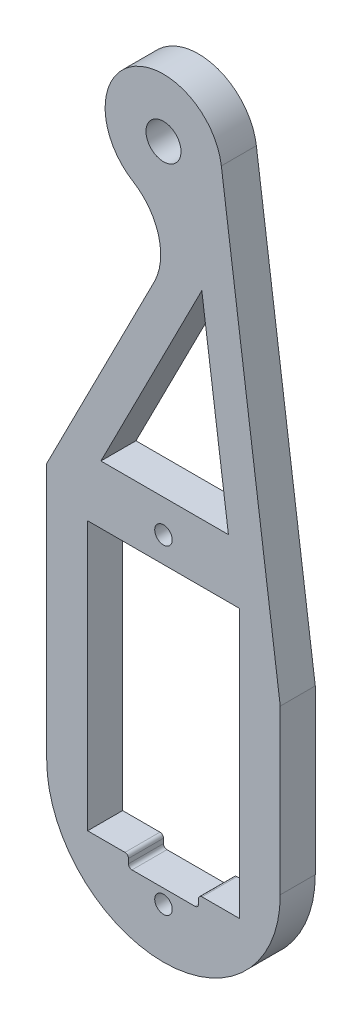
SolidWorks part; units mm, degrees
ref_plane "前视基准面" through (0, 0, 0) normal (0, 0, 1) x (1, 0, 0)
ref_plane "上视基准面" through (0, 0, 0) normal (0, 1, 0) x (1, 0, 0)
ref_plane "右视基准面" through (0, 0, 0) normal (1, 0, 0) x (0, 0, -1)
sketch "草图1" plane through (0, 0, 0) normal (0, 0, 1) x (1, 0, 0)
  line L0 (0, 0) -> (18.9934, 0) construction
  line L1 (-6.5, 11.5) -> (6.5, 11.5)
  line L2 (-6.5, 11.5) -> (-6.5, -11.5)
  line L3 (-6.5, -11.5) -> (6.5, -11.5)
  line L4 (6.5, 11.5) -> (6.5, -11.5)
  line L5 (-6.5, 11.5) -> (6.5, -11.5) construction
  line L6 (-6.5, -11.5) -> (6.5, 11.5) construction
  line L7 (0, 0) -> (0, 13.7) construction
  line L8 (0, -8) -> (0, 0) construction
  line L9 (0, 42.88) -> (0, 0) construction
  line L10 (10, -8) -> (10, 6)
  line L11 (10, 6) -> (4.9555, 43.5458)
  line L12 (-10, -8) -> (-10, 14)
  line L13 (-10, 14) -> (-0.7821, 32.0911)
  line L14 (-5.3592, 16.5) -> (3.2833, 33.462)
  line L15 (5.5623, 16.5) -> (3.2833, 33.462)
  line L16 (-7.327, 12.638) -> (1.8909, 30.7291) construction
  line L17 (7.0267, 5.6005) -> (1.9822, 43.1463) construction
  line L18 (-5.3592, 16.5) -> (5.5623, 16.5)
  line L19 (-6.5, 16.5) -> (6.5, 16.5) construction
  circle A0 centre (0, 13.7) radius 0.75
  circle A1 centre (0, -13.7) radius 0.75
  arc A2 (-10, -8) -> (10, -8) centre (0, -8) ccw
  arc A3 (4.9555, 43.5458) -> (0, 37.88) centre (0, 42.88) ccw
  circle A4 centre (0, -5.12) radius 4 construction
  arc A5 (-0.7821, 32.0911) -> (-2.6186, 38.6205) centre (-5.2372, 34.3611) ccw
  circle A6 centre (0, 42.88) radius 1.5
  point P0 (0, 0)
  point P13 (0, 0)
  dimension "D3" = 1.5
  dimension "D5" = 10
  dimension "D7" = 10
  dimension "D10" = 8
  dimension "D13" = 10
  dimension "D14" = 63
  dimension "D18" = 3
  dimension "D1" = 23
  dimension "D2" = 13
  dimension "D4" = 27.4
  dimension "D6" = 8
  dimension "D8" = 6.38
  dimension "D9" = 48
  dimension "D11" = 14
  dimension "D12" = 22
  dimension "D15" = 3
  dimension "D16" = 3
  dimension "D17" = 5
extrude "凸台-拉伸1" add sketch "草图1" along normal mid plane 3
sketch "草图2" plane through (0, 0, 1.5) normal (0, 0, 1) x (1, 0, 0)
  line L0 (-3, -11.5) -> (-3, -12.5)
  line L1 (-6.5, -11.5) -> (6.5, -11.5) construction
  line L2 (-3, -12.5) -> (3, -12.5)
  line L3 (3, -12.5) -> (3, -11.5)
  line L4 (0, -11.5) -> (0, -9.1202) construction
  line L5 (3, -11.5) -> (-3, -11.5)
  dimension "D1" = 6
  dimension "D2" = 1
extrude "切除-拉伸1" cut sketch "草图2" against normal blind 3
fillet "圆角1" radius 0.3 4 edges at (3, -12.5, 0) (3, -11.5, 0) (-3, -12.5, 0) (-3, -11.5, 0)
